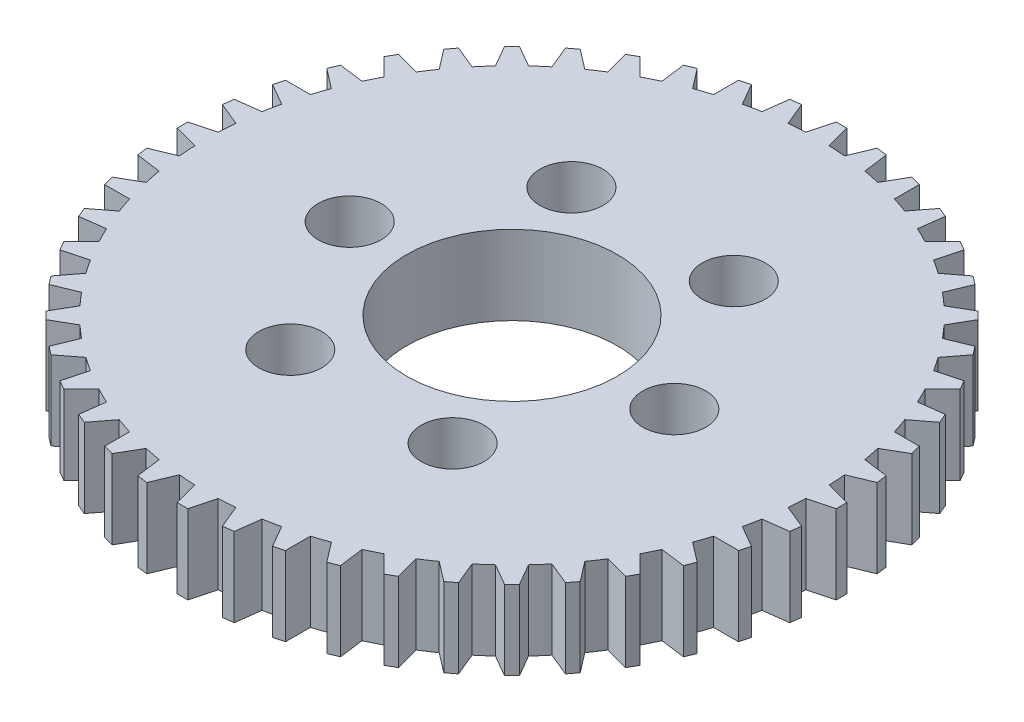
SolidWorks part; units mm, degrees
material "6061-T6 (SS)"
ref_plane "Front Plane" through (0, 0, 0) normal (0, 0, 1) x (1, 0, 0)
ref_plane "Top Plane" through (0, 0, 0) normal (0, 1, 0) x (1, 0, 0)
ref_plane "Right Plane" through (0, 0, 0) normal (1, 0, 0) x (0, 0, -1)
sketch "Sketch1" plane through (0, 0, 0) normal (0, 1, 0) x (1, 0, 0)
  circle A0 centre (0, 0) radius 18.415
  circle A1 centre (0, 0) radius 6.35
  dimension "D1" = 36.83
  dimension "D2" = 12.7
extrude "Boss-Extrude1" add sketch "Sketch1" along normal blind 4.7625
sketch "Sketch2" plane through (0, 4.7625, 0) normal (0, 1, 0) x (1, 0, 0)
  line L0 (0, 0) -> (0, 19.8501) construction
  line L1 (-1.1342, 16.8021) -> (1.1342, 16.8021)
  line L2 (-1.1342, 16.8021) -> (-0.3175, 19.8501)
  line L3 (-0.3175, 19.8501) -> (0.3175, 19.8501)
  line L4 (0.3175, 19.8501) -> (1.1342, 16.8021)
  dimension "D1" = 19.8501
  dimension "D2" = 0.635
  dimension "D3" = 75
  dimension "D4" = 3.048
extrude "Boss-Extrude2" add sketch "Sketch2" against normal up to surface (4.7625 mm away) up to face at (0, 0, 18.415)
pattern_circular "CirPattern1" count 48 over 360 about axis through (0, 0, 0) along (0, 1, 0) of "Boss-Extrude2"
hole_wizard "#6 Clearance Hole1" positions "Sketch3" profile "Sketch4" hole size "#6" standard "ANSI Inch" end condition through all
sketch "Sketch3" plane through (0, 4.7625, 0) normal (0, 1, 0) x (1, 0, 0)
  point P13 (9.779, 0)
  dimension "D1" = 9.779
sketch "Sketch4" plane through (9.779, 4.7625, 0) normal (1, 0, 0) x (0, 0, 1)
  line L0 (0, 0) -> (0, 4.7625)
  line L1 (0, 4.7625) -> (1.8986, 4.7625)
  line L2 (1.8986, 4.7625) -> (1.8986, 0)
  line L5 (1.8986, 0) -> (0, 0)
  line L11 (0, -6.35) -> (0, 107.95) construction
  dimension "Thru Hole Dia." = 3.7973
  dimension "Thru Hole Depth" = 4.7625
pattern_circular "CirPattern2" count 6 over 360 about axis through (0, 0, 0) along (0, 1, 0) of "#6 Clearance Hole1"
sketch "Sketch5" plane through (0, 4.7625, 0) normal (0, 1, 0) x (1, 0, 0)
  circle A0 centre (0, 0) radius 19.05 construction
  dimension "D1" = 38.1
